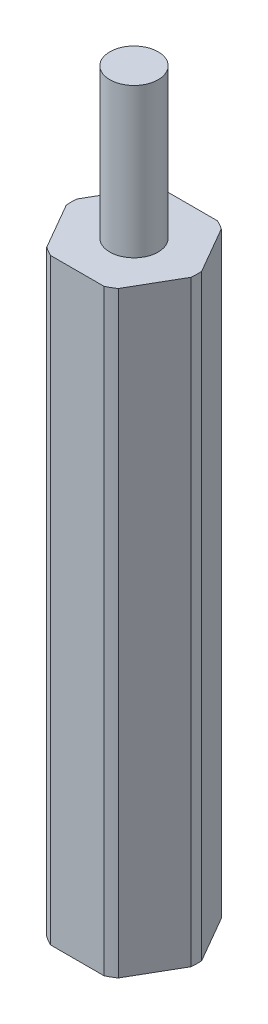
SolidWorks part; units mm, degrees
ref_plane "Front Plane" through (0, 0, 0) normal (0, 0, 1) x (1, 0, 0)
ref_plane "Top Plane" through (0, 0, 0) normal (0, 1, 0) x (1, 0, 0)
ref_plane "Right Plane" through (0, 0, 0) normal (1, 0, 0) x (0, 0, -1)
sketch "Sketch1" plane through (0, 0, 0) normal (0, 1, 0) x (1, 0, 0)
  line L0 (-1.1359, 2.413) -> (1.1359, 2.413)
  line L1 (1.5218, 2.1902) -> (2.6577, 0.2228)
  line L2 (2.6577, -0.2228) -> (1.5218, -2.1902)
  line L3 (1.1359, -2.413) -> (-1.1359, -2.413)
  line L4 (-1.5218, -2.1902) -> (-2.6577, -0.2228)
  line L5 (-2.6577, 0.2228) -> (-1.5218, 2.1902)
  arc A0 (-2.6577, 0.2228) -> (-2.6577, -0.2228) centre (0, 0) ccw
  arc A1 (-1.5218, -2.1902) -> (-1.1359, -2.413) centre (0, 0) ccw
  arc A2 (1.1359, -2.413) -> (1.5218, -2.1902) centre (0, 0) ccw
  arc A3 (2.6577, -0.2228) -> (2.6577, 0.2228) centre (0, 0) ccw
  arc A4 (1.5218, 2.1902) -> (1.1359, 2.413) centre (0, 0) ccw
  arc A5 (-1.1359, 2.413) -> (-1.5218, 2.1902) centre (0, 0) ccw
  point P18 (0, 0)
  dimension "D1" = 5.334
  dimension "D2" = 2.413
  dimension "D3" = 6
extrude "Boss-Extrude1" add sketch "Sketch1" along normal blind 25.4
sketch "Sketch2" plane through (0, 25.4, 0) normal (0, 1, 0) x (1, 0, 0)
  circle A0 centre (0, 0) radius 1.0287
  dimension "D1" = 2.0574
extrude "Boss-Extrude2" add sketch "Sketch2" along normal blind 6.35
sketch "Sketch3" plane through (0, 0, 0) normal (0, -1, 0) x (1, 0, 0)
  circle A0 centre (0, 0) radius 1.0287
  dimension "D1" = 2.0574
extrude "Cut-Extrude1" cut sketch "Sketch3" against normal blind 6.35
equation "\"D2@Sketch1\"=(.19/2)\""
